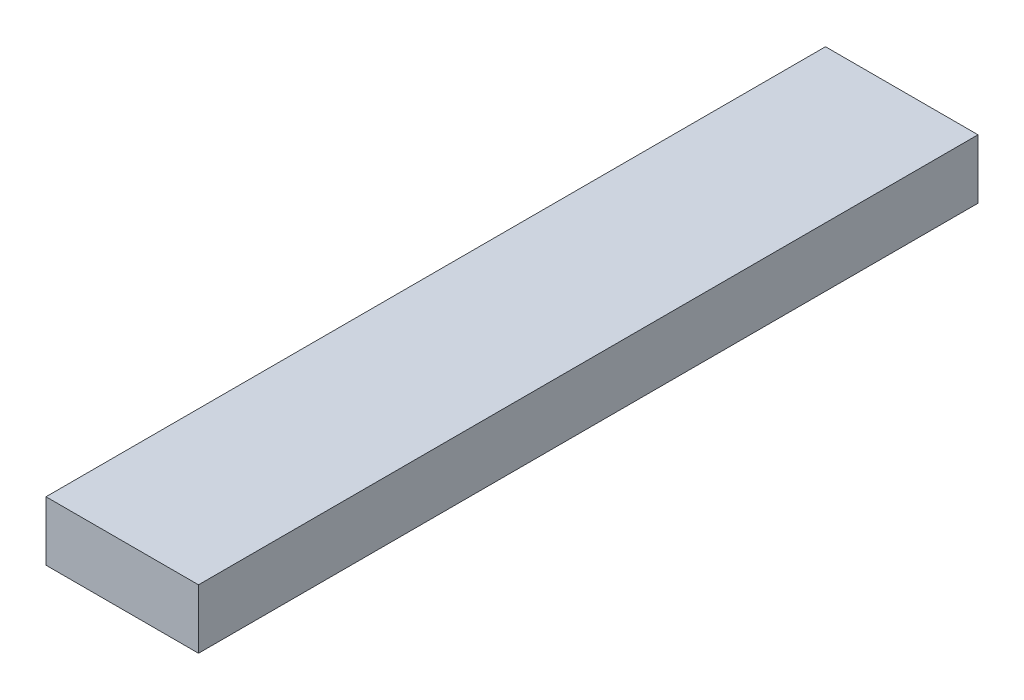
SolidWorks part; units mm, degrees
ref_plane "Alzado" through (0, 0, 0) normal (0, 0, 1) x (1, 0, 0)
ref_plane "Planta" through (0, 0, 0) normal (0, 1, 0) x (1, 0, 0)
ref_plane "Vista lateral" through (0, 0, 0) normal (1, 0, 0) x (0, 0, -1)
sketch "Croquis1" plane through (0, 0, 0) normal (0, 0, 1) x (1, 0, 0)
  line L0 (-71.5549, 9.0177) -> (-62.5549, 9.0177)
  line L1 (-62.5549, 9.0177) -> (-62.5549, 5.5177)
  line L2 (-62.5549, 5.5177) -> (-71.5549, 5.5177)
  line L3 (-71.5549, 5.5177) -> (-71.5549, 9.0177)
extrude "Saliente-Extruir1" add sketch "Croquis1" along normal blind 46
